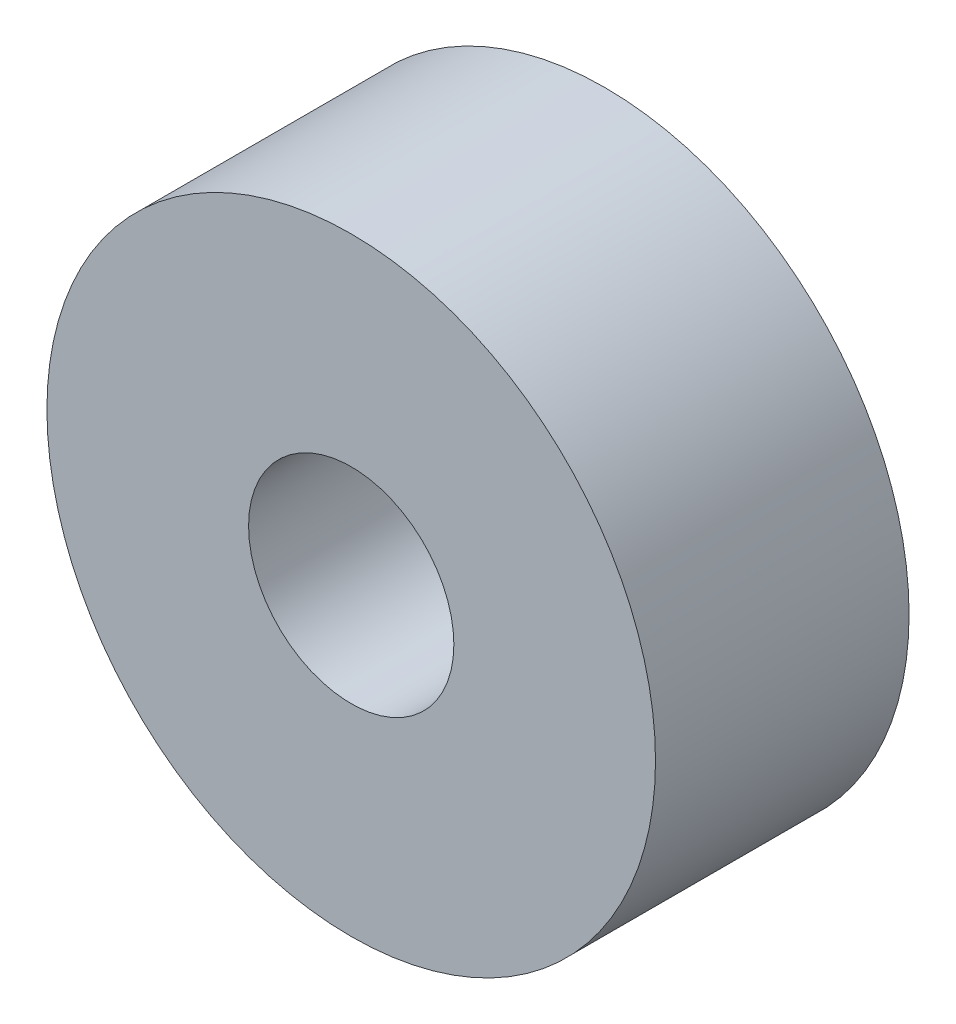
SolidWorks part; units mm, degrees
material "PBT General Purpose"
ref_plane "Front Plane" through (0, 0, 0) normal (0, 0, 1) x (1, 0, 0)
ref_plane "Top Plane" through (0, 0, 0) normal (0, 1, 0) x (1, 0, 0)
ref_plane "Right Plane" through (0, 0, 0) normal (1, 0, 0) x (0, 0, -1)
sketch "Sketch1" plane through (0, 0, 0) normal (0, 0, 1) x (1, 0, 0)
  circle A0 centre (0, 0) radius 1.6065
  circle A1 centre (0, 0) radius 4.7625
  dimension "D1" = 3.2131
  dimension "D2" = 9.525
extrude "Boss-Extrude1" add sketch "Sketch1" along normal blind 3.9688
